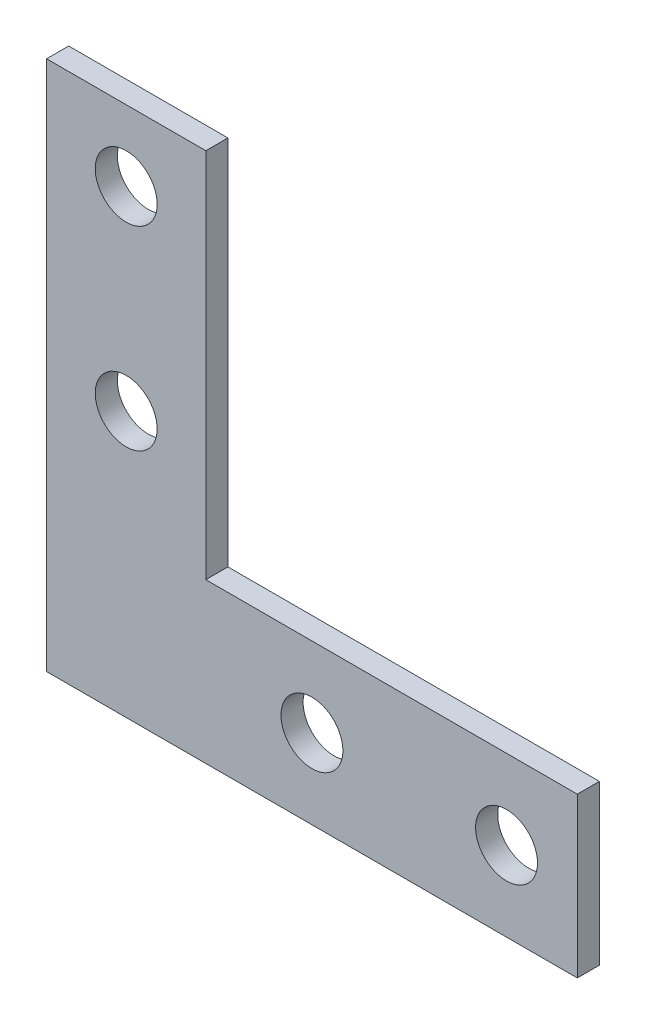
SolidWorks part; units mm, degrees
ref_plane "Спереди" through (0, 0, 0) normal (0, 0, 1) x (1, 0, 0)
ref_plane "Сверху" through (0, 0, 0) normal (0, 1, 0) x (1, 0, 0)
ref_plane "Справа" through (0, 0, 0) normal (1, 0, 0) x (0, 0, -1)
sketch "Эскиз1" plane through (0, 0, 0) normal (0, 0, 1) x (1, 0, 0)
  line L5 (0, 60) -> (0, 0)
  line L6 (0, 0) -> (60, 0)
  line L11 (60, 0) -> (60, 18)
  line L12 (60, 18) -> (18, 18)
  line L16 (18, 18) -> (18, 60)
  line L17 (18, 60) -> (0, 60)
  line L18 (60, 9) -> (52, 9) construction
  line L19 (52, 9) -> (30, 9) construction
  line L20 (9, 60) -> (9, 52) construction
  line L21 (9, 52) -> (9, 30) construction
  circle A6 centre (9, 52) radius 3.5
  circle A7 centre (9, 30) radius 3.5
  circle A8 centre (30, 9) radius 3.5
  circle A9 centre (52, 9) radius 3.5
  dimension "D4" = 8
  dimension "D5" = 22
  dimension "D3" = 7
  dimension "D1" = 60
  dimension "D2" = 18
extrude "Бобышка-Вытянуть1" add sketch "Эскиз1" along normal blind 2.5
